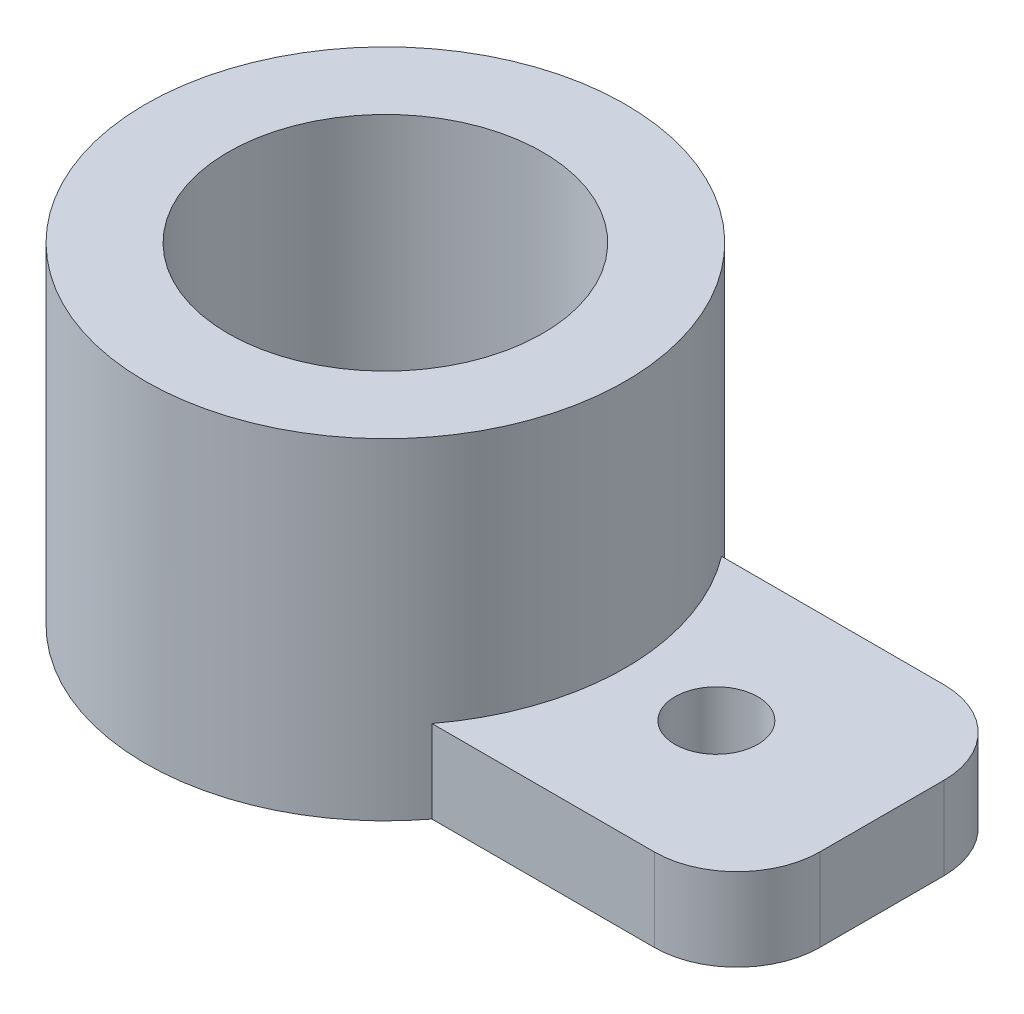
SolidWorks part; units mm, degrees
ref_plane "Front" through (0, 0, 0) normal (0, 0, 1) x (1, 0, 0)
ref_plane "Top" through (0, 0, 0) normal (0, 1, 0) x (1, 0, 0)
ref_plane "Right" through (0, 0, 0) normal (1, 0, 0) x (0, 0, -1)
sketch "草图1" plane through (0, 0, 0) normal (0, 1, 0) x (1, 0, 0)
  line L0 (-12.8608, 0) -> (15.3394, 0) construction
  circle A0 centre (0, 0) radius 2.9
  dimension "D1" = 5.8
extrude "凸台-拉伸1" add sketch "草图1" along normal blind 4
sketch "草图2" plane through (0, 0, 0) normal (0, 1, 0) x (1, 0, 0)
  line L0 (-6.7906, 0) -> (11.2096, 0) construction
  line L2 (14, -1.75) -> (1.3719, -1.75)
  line L3 (14, -1.75) -> (14, 1.75)
  line L4 (14, 1.75) -> (1.3719, 1.75)
  line L5 (1.3719, -1.75) -> (1.3719, 1.75)
  line L6 (14, -1.75) -> (1.3719, 1.75) construction
  line L7 (14, 1.75) -> (1.3719, -1.75) construction
  point P3 (7.686, 0)
  dimension "D1" = 3.5
  dimension "D2" = 14
extrude "凸台-拉伸2" add sketch "草图2" along normal blind 1
sketch "草图3" plane through (0, 0, 0) normal (0, 1, 0) x (1, 0, 0)
  line L0 (-7.4712, 0) -> (17.1185, 0) construction
  circle A0 centre (8, 0) radius 0.5
  circle A1 centre (12, 0) radius 0.5
  circle A2 centre (10, 0) radius 0.5
  circle A3 centre (0, 0) radius 1
  circle A5 centre (4, 0) radius 0.5
  dimension "D1" = 1
  dimension "D2" = 1
  dimension "D3" = 1
  dimension "D7" = 2
  dimension "D8" = 1
  dimension "D4" = 8
  dimension "D5" = 2
  dimension "D6" = 2
  dimension "D9" = 4
extrude "切除-拉伸1" cut sketch "草图3" along normal through all
fillet "圆角1" radius 1.5 2 edges at (14, 0.5, 1.75) (14, 0.5, -1.75)
sketch "草图4" plane through (0, 4, 0) normal (0, 1, 0) x (1, 0, 0)
  circle A0 centre (0, 0) radius 1.9
  dimension "D1" = 3.8
extrude "切除-拉伸2" cut sketch "草图4" against normal blind 3
sketch "草图5" plane through (0, 1, 0) normal (0, 1, 0) x (1, 0, 0)
  line L0 (12.5, 1.75) -> (2.3125, 1.75) construction
  line L1 (6, 1.75) -> (15.1166, 1.75)
  line L2 (6, 1.75) -> (6, -1.75)
  line L3 (6, -1.75) -> (15.1166, -1.75)
  line L4 (15.1166, 1.75) -> (15.1166, -1.75)
  line L5 (2.3125, -1.75) -> (12.5, -1.75) construction
  dimension "D1" = 6
extrude "切除-拉伸3" cut sketch "草图5" against normal through all
fillet "圆角2" radius 1 2 edges at (6, 0.5, 1.75) (6, 0.5, -1.75)
